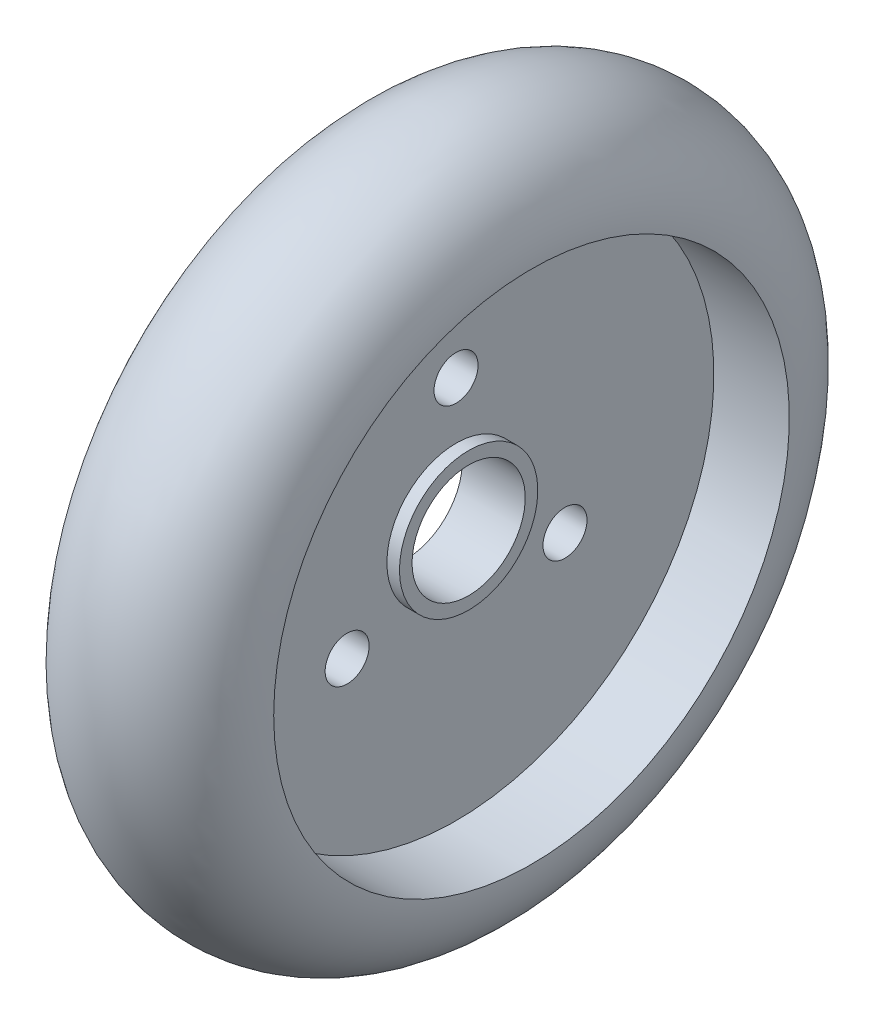
SolidWorks part; units mm, degrees
ref_plane "正面(Front)" through (0, 0, 0) normal (0, 0, 1) x (1, 0, 0)
ref_plane "平面(Top)" through (0, 0, 0) normal (0, 1, 0) x (1, 0, 0)
ref_plane "右側面(Right)" through (0, 0, 0) normal (1, 0, 0) x (0, 0, -1)
sketch "ｽｹｯﾁ1" plane through (0, 0, 0) normal (0, 0, 1) x (1, 0, 0)
  line L0 (0, 0) -> (0, 29.563) construction
  line L1 (0, 0) -> (19.4862, 0) construction
  line L2 (-2.5, 4.5) -> (2.5, 4.5)
  line L3 (2.5, 4.5) -> (2.5, 5.5)
  line L4 (2.5, 5.5) -> (1.5, 5.5)
  line L5 (1.5, 5.5) -> (1.5, 20.5)
  line L6 (1.5, 20.5) -> (7.5, 20.5)
  line L7 (-1.5, 20.5) -> (-7.5, 20.5)
  line L8 (-1.5, 5.5) -> (-1.5, 20.5)
  line L9 (-2.5, 5.5) -> (-1.5, 5.5)
  line L10 (-2.5, 4.5) -> (-2.5, 5.5)
  arc A0 (7.5, 20.5) -> (-7.5, 20.5) centre (0, 20.5) ccw
  point P24 (0, 4.5)
  dimension "D1" = 56
  dimension "D2" = 15
  dimension "D3" = 6
  dimension "D4" = 11
  dimension "D5" = 1
  dimension "D6" = 1
revolve "回転1" add sketch "ｽｹｯﾁ1" angle 360 about L1
sketch "ｽｹｯﾁ2" plane through (0, 0, 0) normal (1, 0, 0) x (0, 0, -1)
  line L0 (0, 0) -> (0, 10) construction
  circle A0 centre (0, 10) radius 1.75
  circle A1 centre (8.6603, -5) radius 1.75
  circle A2 centre (-8.6603, -5) radius 1.75
  dimension "D1" = 3.5
  dimension "D2" = 10
  dimension "D4" = 10
  dimension "D3" = 3
extrude "ｶｯﾄ - 押し出し1" cut sketch "ｽｹｯﾁ2" against normal through all both and the other way through all
